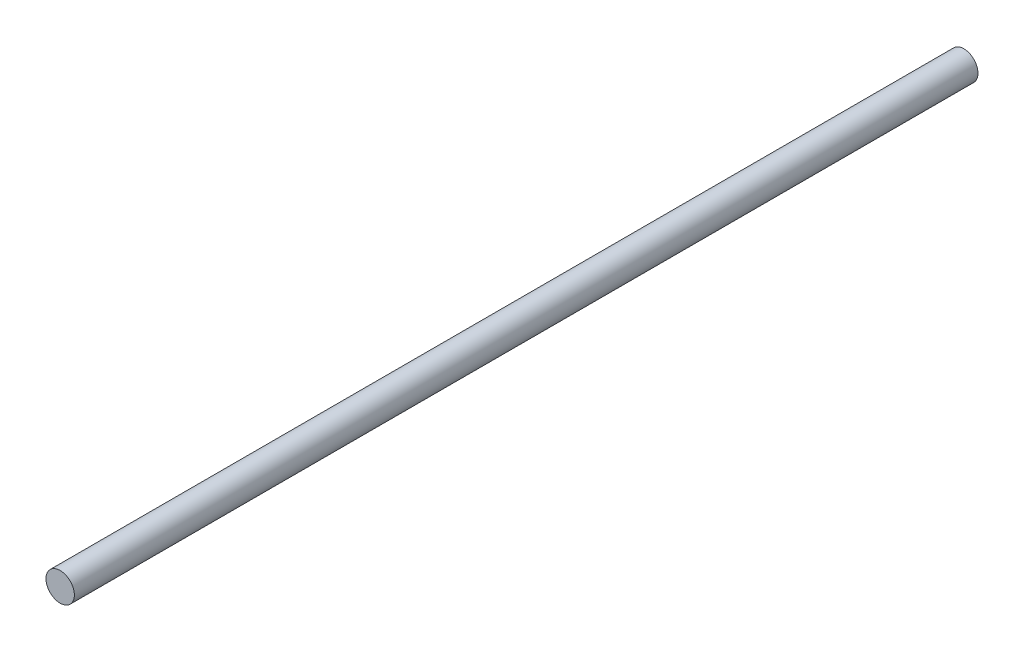
SolidWorks part; units mm, degrees
ref_plane "Front Plane" through (0, 0, 0) normal (0, 0, 1) x (1, 0, 0)
ref_plane "Top Plane" through (0, 0, 0) normal (0, 1, 0) x (1, 0, 0)
ref_plane "Right Plane" through (0, 0, 0) normal (1, 0, 0) x (0, 0, -1)
sketch "Sketch1" plane through (0, 0, 0) normal (0, 0, 1) x (1, 0, 0)
  circle A0 centre (0, 0) radius 3.9878
  dimension "D1" = 7.9756
extrude "Boss-Extrude1" add sketch "Sketch1" along normal blind 254 contours A0
